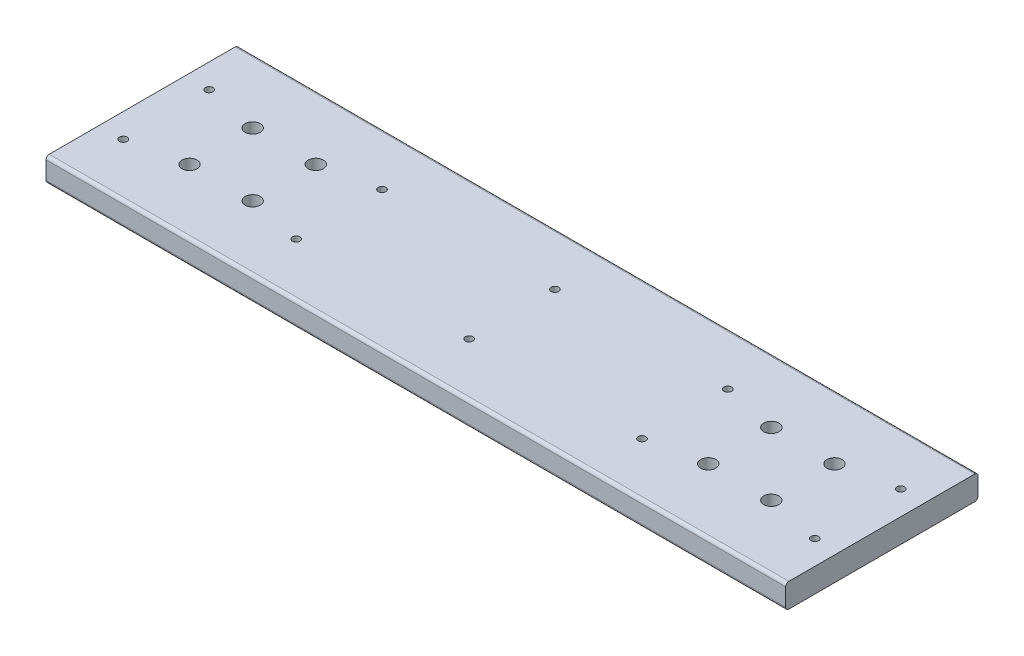
SolidWorks part; units mm, degrees
material "6061 Alloy"
ref_plane "Front Plane" through (0, 0, 0) normal (0, 0, 1) x (1, 0, 0)
ref_plane "Top Plane" through (0, 0, 0) normal (0, 1, 0) x (1, 0, 0)
ref_plane "Right Plane" through (0, 0, 0) normal (1, 0, 0) x (0, 0, -1)
sketch "Sketch1" plane through (0, 0, 0) normal (1, 0, 0) x (0, 0, -1)
  line L1 (-38.1, 9.525) -> (38.1, 9.525)
  line L2 (-38.1, 9.525) -> (-38.1, 0)
  line L3 (-38.1, 0) -> (38.1, 0)
  line L4 (38.1, 9.525) -> (38.1, 0)
  point P4 (0, 0)
  dimension "D1" = 9.525
  dimension "D2" = 76.2
extrude "Boss-Extrude1" add sketch "Sketch1" along normal mid plane 293.05
hole_wizard "Ø3.0mm Dowel Hole2" positions "Sketch2" profile "Sketch3" hole size "Ø3.0" standard "ANSI Metric" end condition through all
sketch "Sketch2" plane through (0, 9.525, 0) normal (0, 1, 0) x (1, 0, 0)
  point P0 (-137, 17)
  point P2 (-137, -17)
  point P4 (-68.5, 17)
  point P6 (-68.5, -17)
  point P8 (0, 17)
  point P10 (0, -17)
  point P12 (68.5, 17)
  point P14 (68.5, -17)
  point P16 (137, 17)
  point P18 (137, -17)
  dimension "D1" = 34
  dimension "D2" = 17
  dimension "D3" = 137
  dimension "D4" = 68.5
  dimension "D5" = 137
  dimension "D6" = 137
sketch "Sketch3" plane through (-137, 9.525, -17) normal (1, 0, 0) x (0, 0, 1)
  line L0 (0, 0) -> (0, 9.525)
  line L1 (0, 9.525) -> (1.5, 9.525)
  line L2 (1.5, 9.525) -> (1.5, 0)
  line L5 (1.5, 0) -> (0, 0)
  line L11 (0, -6.35) -> (0, 107.95) construction
  dimension "Thru Hole Dia." = 3
  dimension "Thru Hole Depth" = 9.525
fillet "Fillet1" radius 1.27 4 edges at (0, 0, -38.1) (0, 9.525, -38.1) (0, 9.525, 38.1) (0, 0, 38.1)
hole_wizard "Ø6.0mm Dowel Hole2" positions "Sketch5" profile "Sketch6" hole size "Ø6.0" standard "ANSI Metric" end condition through all
sketch "Sketch5" plane through (0, 9.525, 0) normal (0, 1, 0) x (1, 0, 0)
  line L2 (-115.25, 12.5) -> (-90.25, 12.5) construction
  line L3 (-115.25, 12.5) -> (-115.25, -12.5) construction
  line L4 (-115.25, -12.5) -> (-90.25, -12.5) construction
  line L5 (-90.25, 12.5) -> (-90.25, -12.5) construction
  line L7 (90.25, 12.5) -> (115.25, 12.5) construction
  line L8 (90.25, 12.5) -> (90.25, -12.5) construction
  line L9 (90.25, -12.5) -> (115.25, -12.5) construction
  line L10 (115.25, 12.5) -> (115.25, -12.5) construction
  line L11 (-137, 17) -> (-68.5, 17) construction
  line L13 (68.5, 17) -> (137, 17) construction
  circle A6 centre (-68.5, 17) radius 1.5 construction
  circle A7 centre (-68.5, 17) radius 1.5
  circle A8 centre (68.5, 17) radius 1.5 construction
  circle A9 centre (68.5, 17) radius 1.5
  circle A10 centre (-137, 17) radius 1.5 construction
  circle A11 centre (-137, 17) radius 1.5
  circle A12 centre (137, 17) radius 1.5 construction
  circle A13 centre (137, 17) radius 1.5
  point P0 (-115.25, 12.5)
  point P2 (-115.25, -12.5)
  point P4 (-90.25, 12.5)
  point P6 (-90.25, -12.5)
  point P8 (90.25, 12.5)
  point P10 (90.25, -12.5)
  point P12 (115.25, 12.5)
  point P14 (115.25, -12.5)
  point P143 (90.25, 0)
  point P144 (-90.25, 0)
  point P147 (-102.75, 12.5)
  point P152 (102.75, 12.5)
  point P166 (-102.75, 17)
  point P167 (102.75, 17)
  dimension "D1" = 25
  dimension "D2" = 25
sketch "Sketch6" plane through (-115.25, 9.525, -12.5) normal (1, 0, 0) x (0, 0, 1)
  line L0 (0, 0) -> (0, 9.525)
  line L1 (0, 9.525) -> (3, 9.525)
  line L2 (3, 9.525) -> (3, 0)
  line L5 (3, 0) -> (0, 0)
  line L11 (0, -6.35) -> (0, 107.95) construction
  dimension "Thru Hole Dia." = 6
  dimension "Thru Hole Depth" = 9.525
hole_wizard "Ø6.0mm Dowel Hole1" positions "Sketch7" profile "Sketch8" hole size "Ø6.0" standard "ANSI Metric"
sketch "Sketch7" plane through (0, 9.525, 0) normal (0, 1, 0) x (1, 0, 0)
  line L1 (-86, 25) -> (-51, 25) construction
  line L2 (-86, 25) -> (-86, -25) construction
  line L3 (-86, -25) -> (-51, -25) construction
  line L4 (-51, 25) -> (-51, -25) construction
  line L6 (51, 25) -> (86, 25) construction
  line L7 (51, 25) -> (51, -25) construction
  line L8 (51, -25) -> (86, -25) construction
  line L9 (86, 25) -> (86, -25) construction
  circle A0 centre (-68.5, 17) radius 2.4574 construction
  circle A1 centre (-68.5, 17) radius 2.4574
  circle A2 centre (68.5, 17) radius 2.4574 construction
  circle A3 centre (68.5, 17) radius 2.4574
  point P0 (-86, 25)
  point P2 (-86, -25)
  point P4 (-51, -25)
  point P6 (-51, 25)
  point P8 (51, 25)
  point P10 (51, -25)
  point P12 (86, -25)
  point P14 (86, 25)
  point P100 (-68.5, 25)
  point P102 (68.5, 25)
  point P103 (-51, 0)
  point P105 (51, 0)
  dimension "D1" = 35
  dimension "D2" = 50
sketch "Sketch8" plane through (-86, 9.525, -25) normal (1, 0, 0) x (0, 0, 1)
  line L0 (0, 0) -> (0, 9.525)
  line L1 (0, 9.525) -> (3, 9.525)
  line L2 (3, 9.525) -> (3, 0)
  line L5 (3, 0) -> (0, 0)
  line L11 (0, -6.35) -> (0, 107.95) construction
  dimension "Thru Hole Dia." = 6
  dimension "Thru Hole Depth" = 9.525
equation "\"D2@Sketch2\"=\"D1@Sketch2\"/2"
equation "\"D4@Sketch2\"=\"D3@Sketch2\"/2"
equation "\"D6@Sketch2\"=\"D5@Sketch2\""
